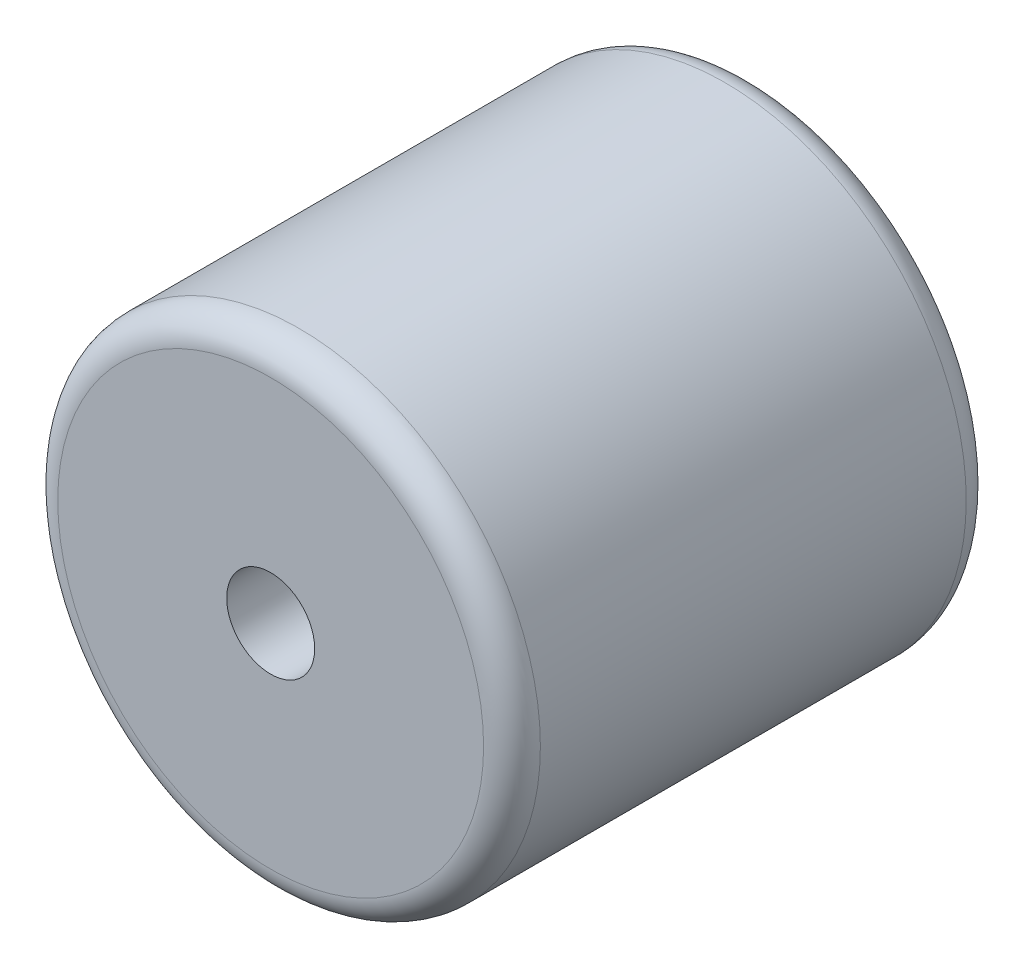
SolidWorks part; units mm, degrees
ref_plane "Front Plane" through (0, 0, 0) normal (0, 0, 1) x (1, 0, 0)
ref_plane "Top Plane" through (0, 0, 0) normal (0, 1, 0) x (1, 0, 0)
ref_plane "Right Plane" through (0, 0, 0) normal (1, 0, 0) x (0, 0, -1)
sketch "Sketch1" plane through (0, 0, 0) normal (0, 0, 1) x (1, 0, 0)
  circle A0 centre (0, 0) radius 8.5
  circle A1 centre (0, 0) radius 1.55
  dimension "D1" = 17
  dimension "D2" = 3.1
extrude "Boss-Extrude1" add sketch "Sketch1" along normal mid plane 17
fillet "Fillet1" radius 1 2 edges at (8.5, 0, -8.5) (8.5, 0, 8.5)
